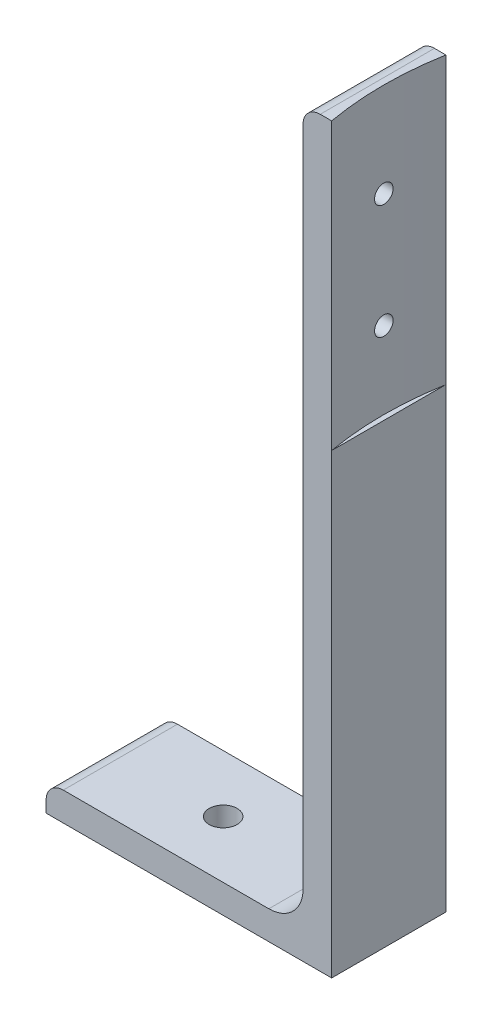
SolidWorks part; units mm, degrees
ref_plane "Front Plane" through (0, 0, 0) normal (0, 0, 1) x (1, 0, 0)
ref_plane "Top Plane" through (0, 0, 0) normal (0, 1, 0) x (1, 0, 0)
ref_plane "Right Plane" through (0, 0, 0) normal (1, 0, 0) x (0, 0, -1)
sketch "Sketch1" plane through (0, 0, 0) normal (0, 0, 1) x (1, 0, 0)
  line L0 (0, 0) -> (0, 130)
  line L1 (-2, 130) -> (0, 130)
  line L2 (-5, 127) -> (-5, 11)
  line L7 (-11, 5) -> (-47, 5)
  line L9 (0, 0) -> (-50, 0)
  line L10 (-50, 2) -> (-50, 0)
  arc A0 (-47, 5) -> (-50, 2) centre (-47, 2) ccw
  arc A1 (-2, 130) -> (-5, 127) centre (-2, 127) ccw
  arc A2 (-5, 11) -> (-11, 5) centre (-11, 11) cw
  point P0 (0, 0)
  point P3 (0, 0)
  point P15 (-5, 130)
  point P19 (0, 0)
  point P20 (-44.8673, -1.6836)
  point P21 (5.3352, 4.1729)
  point P22 (-3.1445, 6.3492)
  dimension "D1" = 3
  dimension "D6" = 3
  dimension "D7" = 6
  dimension "D2" = 5
  dimension "D3" = 5
  dimension "D4" = 130
  dimension "D5" = 50
extrude "Boss-Extrude1" add sketch "Sketch1" along normal mid plane 20
ref_plane "Plane1" through (0, 130, 0) normal (0, 1, 0) x (1, 0, 0)
sketch "Sketch2" plane through (0, 130, 0) normal (0, 1, 0) x (1, 0, 0)
  line L0 (0, -10) -> (0, 10) construction
  line L1 (0, -10) -> (0, 10)
  circle A0 centre (56.116, 0) radius 57
  point P2 (30.2091, 0)
  point P6 (0, 0)
  dimension "D1" = 114
extrude "Cut-Extrude1" cut sketch "Sketch2" against normal blind 50 contours L1 A0
sketch "Sketch3" plane through (-5, 0, 0) normal (-1, 0, 0) x (0, 0, 1)
  line L0 (10, 80) -> (-10, 80) construction
  line L1 (10, 80) -> (-10, 80)
  line L2 (10, 127) -> (-10, 127) construction
  line L3 (10, 127) -> (-10, 127)
  line L4 (-10, 127) -> (-10, 80)
  line L5 (10, 127) -> (10, 80)
  line L6 (-10, 103.5) -> (10, 103.5) construction
  circle A0 centre (0, 113.5) radius 1.625
  circle A1 centre (0, 93.5) radius 1.625
  point P4 (0, 113.5)
  point P5 (0, 93.5)
  point P9 (0, 103.5)
  dimension "D2" = 3.25
  dimension "D3" = 3.25
  dimension "D1" = 10
extrude "Cut-Extrude2" cut sketch "Sketch3" against normal through all contours A1 | A0
sketch "Sketch8" plane through (0, 5, 0) normal (0, 1, 0) x (1, 0, 0)
  line L0 (-29, 10) -> (-29, -10) construction
  line L4 (-11, 10) -> (-47, 10)
  line L5 (-47, 10) -> (-47, -10)
  line L6 (-47, -10) -> (-11, -10)
  line L7 (-11, -10) -> (-11, 10)
  line L8 (-11, 10) -> (-47, 10)
  line L9 (-47, 10) -> (-47, -10)
  line L10 (-47, -10) -> (-11, -10)
  line L11 (-11, -10) -> (-11, 10)
  circle A0 centre (-29, 0) radius 2.45
  point P7 (-29, 10)
  point P10 (-29, -10)
  dimension "D2" = 4.9
  dimension "D1" = 0
extrude "Cut-Extrude3" cut sketch "Sketch8" against normal through all contours A0
